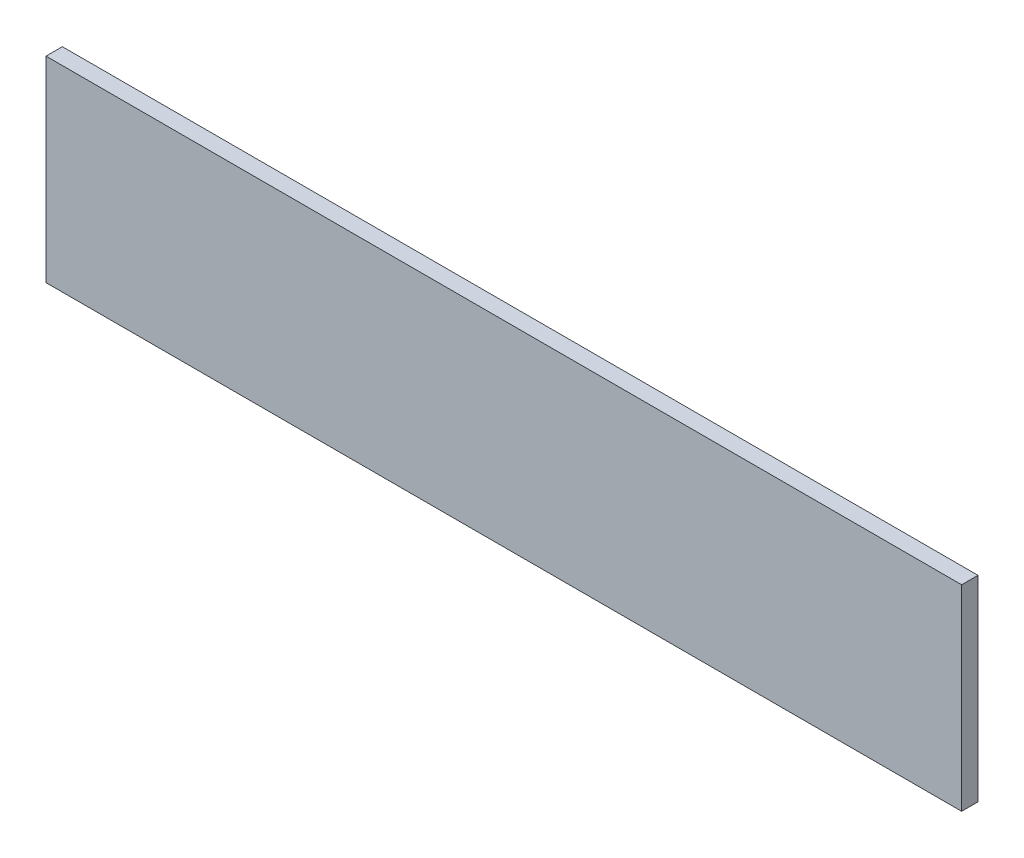
SolidWorks part; units mm, degrees
material "PVC 0.007 Plasticized"
ref_plane "Front Plane" through (0, 0, 0) normal (0, 0, 1) x (1, 0, 0)
ref_plane "Top Plane" through (0, 0, 0) normal (0, 1, 0) x (1, 0, 0)
ref_plane "Right Plane" through (0, 0, 0) normal (1, 0, 0) x (0, 0, -1)
sketch "Sketch1" plane through (0, 0, 0) normal (1, 0, 0) x (0, 0, -1)
  line L1 (-3.175, -38.1) -> (3.175, -38.1)
  line L2 (-3.175, -38.1) -> (-3.175, 38.1)
  line L3 (-3.175, 38.1) -> (3.175, 38.1)
  line L4 (3.175, -38.1) -> (3.175, 38.1)
  line L5 (-3.175, -38.1) -> (3.175, 38.1) construction
  line L6 (-3.175, 38.1) -> (3.175, -38.1) construction
  point P0 (0, 0)
  dimension "D1" = 76.2
  dimension "D2" = 6.35
extrude "Boss-Extrude1" add sketch "Sketch1" along normal blind 355.6
equation "\"D2@Sketch1\"=1in/4"
